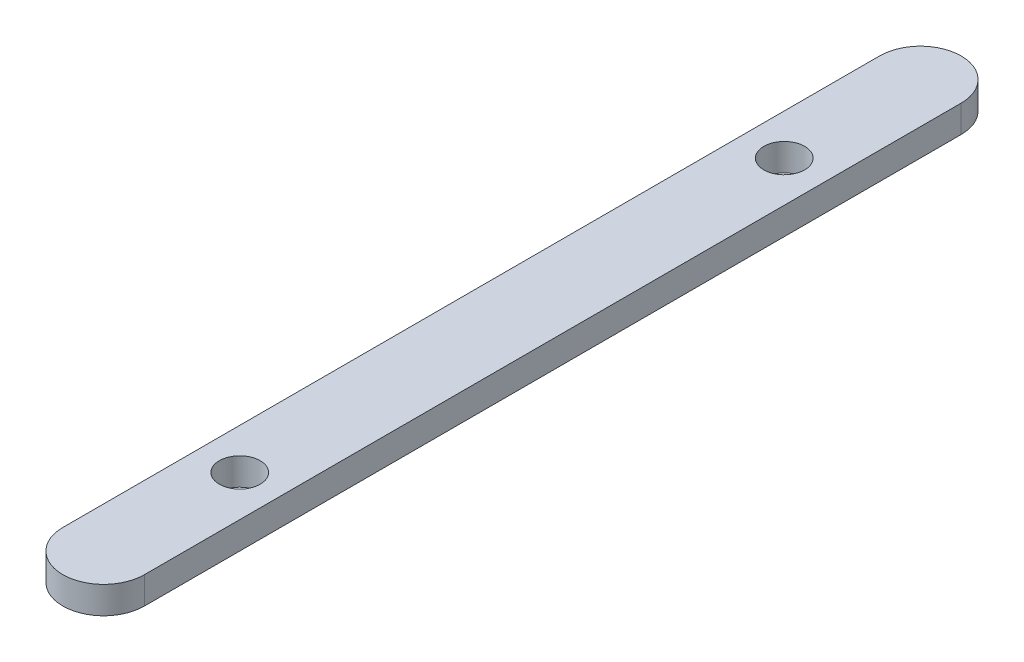
SolidWorks part; units mm, degrees
ref_plane "Front Plane" through (0, 0, 0) normal (0, 0, 1) x (1, 0, 0)
ref_plane "Top Plane" through (0, 0, 0) normal (0, 1, 0) x (1, 0, 0)
ref_plane "Right Plane" through (0, 0, 0) normal (1, 0, 0) x (0, 0, -1)
sketch "Sketch1" plane through (0, 0, 0) normal (0, 1, 0) x (1, 0, 0)
  line L0 (0, -55) -> (0, 55) construction
  line L1 (-3, 30) -> (3, 30)
  line L2 (-3, 30) -> (-3, -30)
  line L3 (-3, -30) -> (3, -30)
  line L4 (3, 30) -> (3, -30)
  line L5 (-55, 0) -> (55, 0) construction
  circle A0 centre (0, 20) radius 1.5
  circle A1 centre (0, -20) radius 1.5
  arc A2 (-3, 30) -> (3, 30) centre (0, 30) cw
  arc A3 (-3, -30) -> (3, -30) centre (0, -30) ccw
  dimension "D5" = 3
  dimension "D6" = 20
  dimension "D1" = 60
  dimension "D2" = 6
  dimension "D3" = 3
  dimension "D4" = 30
  dimension "D7" = 20
extrude "Boss-Extrude1" add sketch "Sketch1" along normal blind 2 contours L4 L1 L2 L3 A1 A0 | L3 A3 | A2 L1
